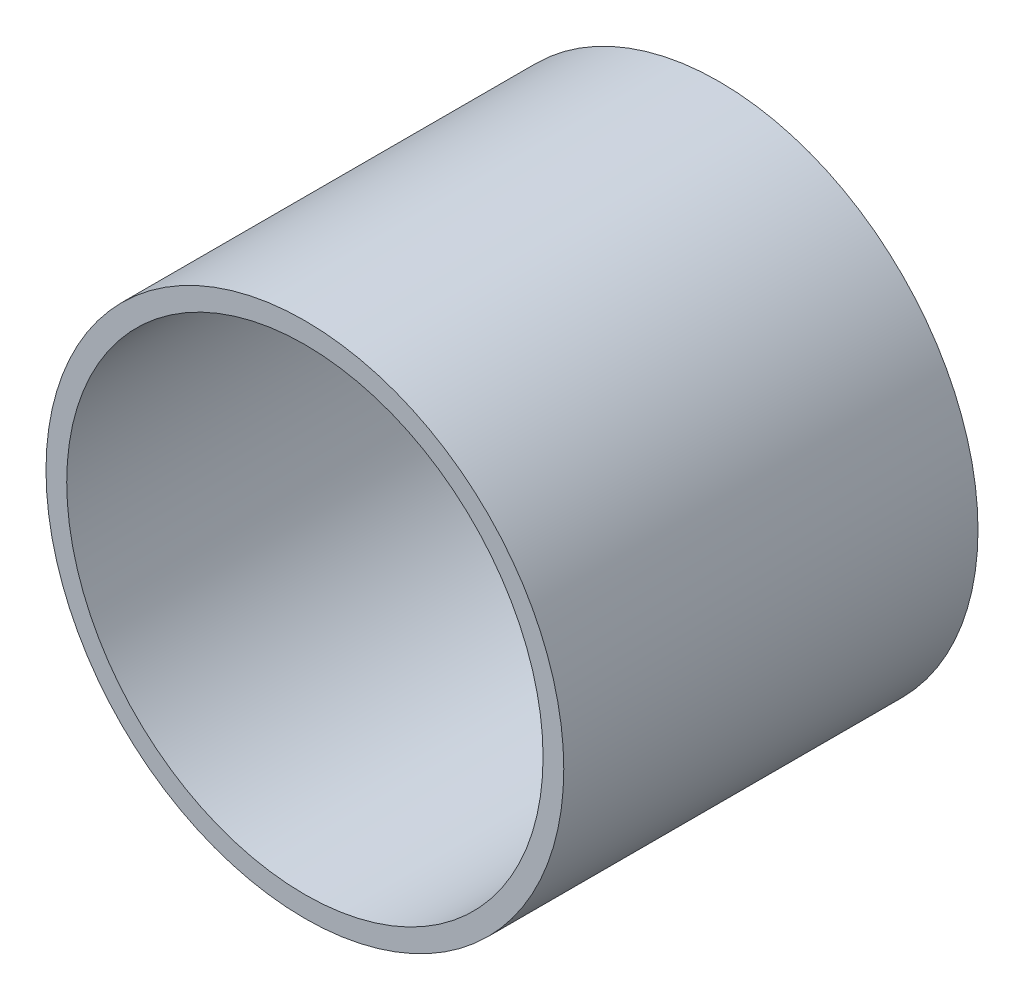
SolidWorks part; units mm, degrees
ref_plane "Front Plane" through (0, 0, 0) normal (0, 0, 1) x (1, 0, 0)
ref_plane "Top Plane" through (0, 0, 0) normal (0, 1, 0) x (1, 0, 0)
ref_plane "Right Plane" through (0, 0, 0) normal (1, 0, 0) x (0, 0, -1)
sketch "Sketch1" plane through (0, 0, 0) normal (0, 0, 1) x (1, 0, 0)
  circle A0 centre (0, 0) radius 73.025
  circle A1 centre (0, 0) radius 79.375
  dimension "D1" = 146.05
  dimension "D2" = 6.35
extrude "Boss-Extrude1" add sketch "Sketch1" along normal blind 127
